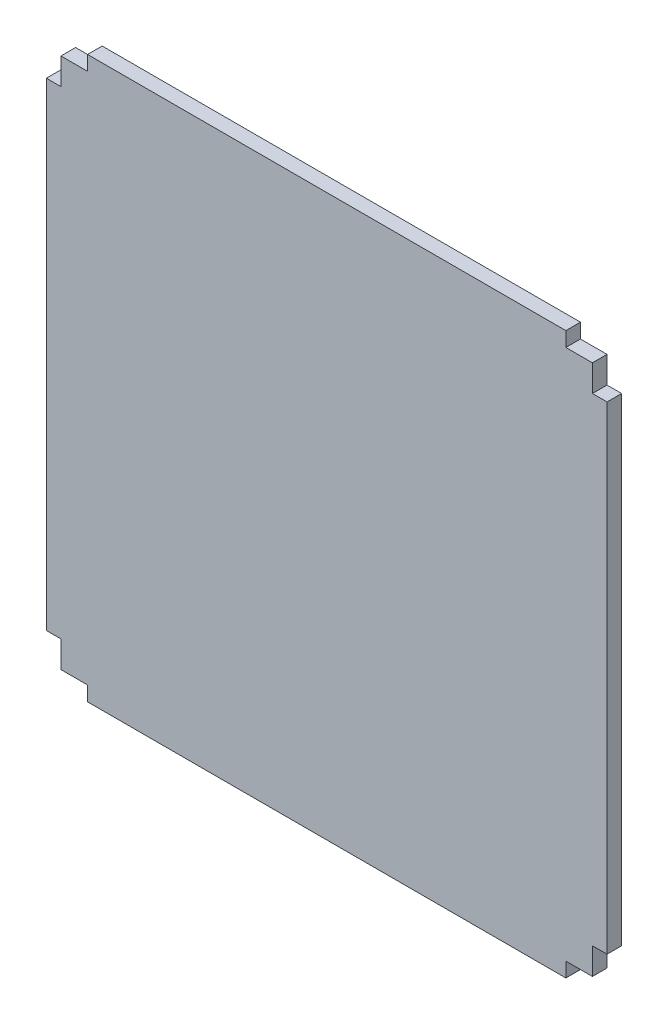
SolidWorks part; units mm, degrees
ref_plane "前视基准面" through (0, 0, 0) normal (0, 0, 1) x (1, 0, 0)
ref_plane "上视基准面" through (0, 0, 0) normal (0, 1, 0) x (1, 0, 0)
ref_plane "右视基准面" through (0, 0, 0) normal (1, 0, 0) x (0, 0, -1)
sketch "草图1" plane through (0, 0, 0) normal (0, 0, 1) x (1, 0, 0)
  line L0 (0, 100) -> (0, 95)
  line L1 (0, 0) -> (100, 0)
  line L2 (0, 0) -> (0, 100)
  line L3 (0, 100) -> (100, 100)
  line L4 (100, 0) -> (100, 100)
  line L5 (0, 95) -> (-2.75, 95)
  line L6 (0, 0) -> (5, 0)
  line L7 (-2.75, 95) -> (0, 95)
  line L8 (-2.75, 95) -> (-2.75, 5)
  line L9 (-2.75, 5) -> (0, 5)
  line L10 (0, 95) -> (0, 5)
  line L11 (100, 0) -> (100, 5)
  line L12 (5, 0) -> (95, 0)
  line L13 (5, 0) -> (5, -2.75)
  line L14 (5, -2.75) -> (95, -2.75)
  line L15 (95, 0) -> (95, -2.75)
  line L16 (100, 5) -> (102.75, 5)
  line L17 (100, 100) -> (95, 100)
  line L18 (102.75, 5) -> (100, 5)
  line L19 (102.75, 5) -> (102.75, 95)
  line L20 (102.75, 95) -> (100, 95)
  line L21 (100, 5) -> (100, 95)
  line L22 (95, 100) -> (95, 102.75)
  line L23 (95, 102.75) -> (5, 102.75)
  line L24 (5, 102.75) -> (5, 100)
extrude "凸台-拉伸1" add sketch "草图1" along normal blind 2.75 contours L1 L4 L3 L0 L2 | L8 L9 L2 L5 | L23 L24 L3 L22 | L19 L20 L4 L16 | L15 L1 L13 L14
